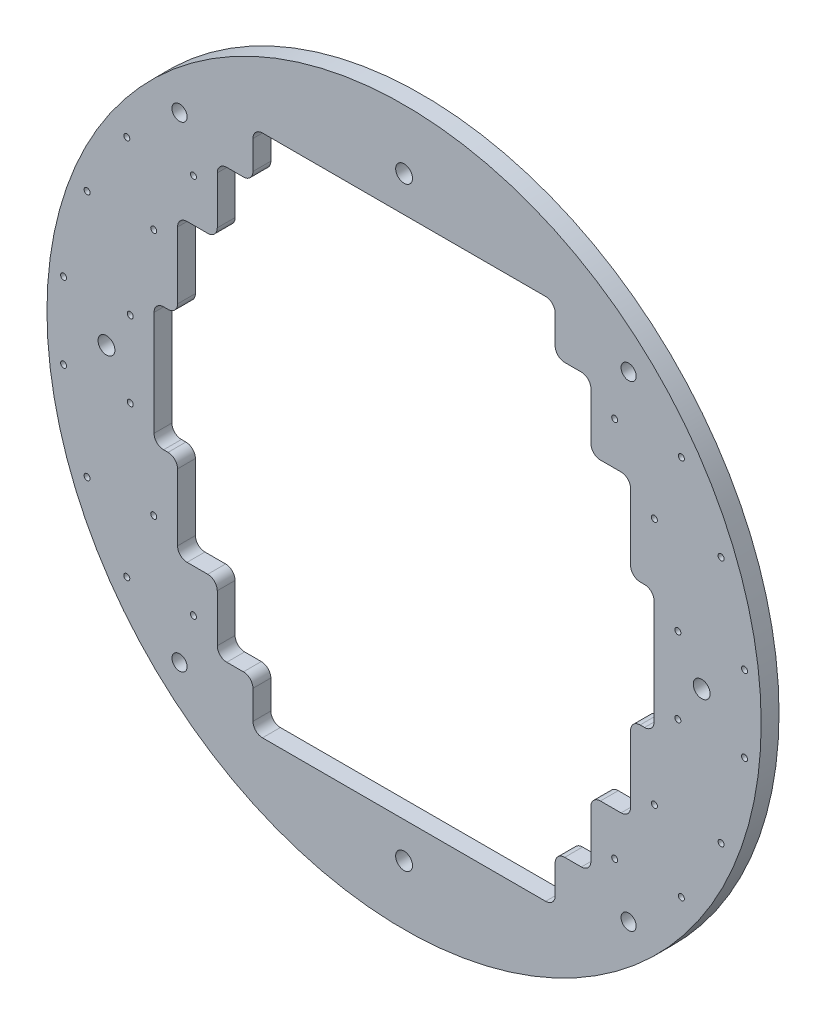
SolidWorks part; units mm, degrees
material "Delrin 2700 NC010, Low Viscosity Acetal Copolymer (SS)"
ref_plane "Front Plane" through (0, 0, 0) normal (0, 0, 1) x (1, 0, 0)
ref_plane "Top Plane" through (0, 0, 0) normal (0, 1, 0) x (1, 0, 0)
ref_plane "Right Plane" through (0, 0, 0) normal (1, 0, 0) x (0, 0, -1)
sketch "Sketch1" plane through (0, 0, 0) normal (0, 0, 1) x (1, 0, 0)
  circle A0 centre (0, 0) radius 95.25
  dimension "D1" = 190.5
extrude "Boss-Extrude1" add sketch "Sketch1" along normal blind 4.7625
hole_wizard "M2x0.4 Tapped Hole1" positions "Sketch3" profile "Sketch2" tap size "M2x0.4" standard "ANSI Metric"
sketch "Sketch3" plane through (0, 0, 4.7625) normal (0, 0, 1) x (1, 0, 0)
  line L0 (-84.5483, 33.02) -> (-66.7683, 33.02) construction
  line L1 (0, 0) -> (-124.3525, 0) construction
  line L2 (-73.9581, 50.8) -> (-56.1781, 50.8) construction
  line L3 (-90.8124, 10.16) -> (-73.0324, 10.16) construction
  line L5 (-73.9581, -50.8) -> (-56.1781, -50.8) construction
  line L6 (-84.5483, -33.02) -> (-66.7683, -33.02) construction
  line L7 (-90.8124, -10.16) -> (-73.0324, -10.16) construction
  line L8 (0, 0) -> (0, 116.1082) construction
  line L10 (73.9581, -50.8) -> (56.1781, -50.8) construction
  line L11 (84.5483, -33.02) -> (66.7683, -33.02) construction
  line L12 (90.8124, -10.16) -> (73.0324, -10.16) construction
  line L13 (90.8124, 10.16) -> (73.0324, 10.16) construction
  line L14 (84.5483, 33.02) -> (66.7683, 33.02) construction
  line L15 (73.9581, 50.8) -> (56.1781, 50.8) construction
  circle A0 centre (0, 0) radius 82.55 construction
  point P0 (-84.5483, 33.02)
  point P2 (-66.7683, 33.02)
  point P19 (-75.6583, 33.02)
  point P25 (-73.9581, 50.8)
  point P27 (-56.1781, 50.8)
  point P34 (-65.0681, 50.8)
  point P35 (-90.8124, 10.16)
  point P37 (-73.0324, 10.16)
  point P44 (-81.9224, 10.16)
  point P45 (-56.1781, -50.8)
  point P46 (-73.9581, -50.8)
  point P48 (-66.7683, -33.02)
  point P49 (-84.5483, -33.02)
  point P51 (-73.0324, -10.16)
  point P52 (-90.8124, -10.16)
  point P60 (56.1781, -50.8)
  point P61 (73.9581, -50.8)
  point P64 (66.7683, -33.02)
  point P65 (84.5483, -33.02)
  point P68 (90.8124, -10.16)
  point P70 (73.0324, -10.16)
  point P71 (90.8124, 10.16)
  point P73 (73.0324, 10.16)
  point P74 (84.5483, 33.02)
  point P76 (66.7683, 33.02)
  point P77 (56.1781, 50.8)
  point P78 (73.9581, 50.8)
  dimension "D4" = 165.1
  dimension "D1" = 17.78
  dimension "D2" = 33.02
  dimension "D3" = 17.78
  dimension "D5" = 50.8
  dimension "D6" = 17.78
  dimension "D7" = 10.16
sketch "Sketch2" plane through (-84.5483, 33.02, 4.7625) normal (1, 0, 0) x (0, -1, 0)
  line L0 (0, 0) -> (0, 5.334)
  line L1 (0, 5.334) -> (0.8, 5.334)
  line L2 (0.8, 5.334) -> (0.8, 0)
  line L5 (0.8, 0) -> (0, 0)
  line L10 (0, 5.334) -> (-0.8, 5.334) construction
  line L11 (0, -6.35) -> (0, 107.95) construction
  dimension "Tap Drill Dia." = 1.6
  dimension "Tap Drill Depth" = 5.334
  dimension "Drill Angle" = 180
cosmetic thread "Hole Thread1" parameters "D1"=4.064, "D2"=2
cosmetic thread "Hole Thread2" parameters "D1"=4.064, "D2"=2
cosmetic thread "Hole Thread3" parameters "D1"=4.064, "D2"=2
cosmetic thread "Hole Thread4" parameters "D1"=4.064, "D2"=2
cosmetic thread "Hole Thread5" parameters "D1"=4.064, "D2"=2
cosmetic thread "Hole Thread6" parameters "D1"=4.064, "D2"=2
cosmetic thread "Hole Thread7" parameters "D1"=4.064, "D2"=2
cosmetic thread "Hole Thread8" parameters "D1"=4.064, "D2"=2
cosmetic thread "Hole Thread9" parameters "D1"=4.064, "D2"=2
cosmetic thread "Hole Thread10" parameters "D1"=4.064, "D2"=2
cosmetic thread "Hole Thread11" parameters "D1"=4.064, "D2"=2
cosmetic thread "Hole Thread12" parameters "D1"=4.064, "D2"=2
cosmetic thread "Hole Thread13" parameters "D1"=4.064, "D2"=2
cosmetic thread "Hole Thread14" parameters "D1"=4.064, "D2"=2
cosmetic thread "Hole Thread15" parameters "D1"=4.064, "D2"=2
cosmetic thread "Hole Thread16" parameters "D1"=4.064, "D2"=2
cosmetic thread "Hole Thread17" parameters "D1"=4.064, "D2"=2
cosmetic thread "Hole Thread18" parameters "D1"=4.064, "D2"=2
cosmetic thread "Hole Thread19" parameters "D1"=4.064, "D2"=2
cosmetic thread "Hole Thread20" parameters "D1"=4.064, "D2"=2
cosmetic thread "Hole Thread21" parameters "D1"=4.064, "D2"=2
cosmetic thread "Hole Thread22" parameters "D1"=4.064, "D2"=2
cosmetic thread "Hole Thread23" parameters "D1"=4.064, "D2"=2
cosmetic thread "Hole Thread24" parameters "D1"=4.064, "D2"=2
hole_wizard "#12-24 Tapped Hole1" positions "Sketch7" profile "Sketch6" tap size "#12-24" standard "ANSI Inch"
sketch "Sketch7" plane through (0, 0, 4.7625) normal (0, 0, 1) x (1, 0, 0)
  circle A0 centre (0, 0) radius 79.375 construction
  point P0 (-79.375, 0)
  point P2 (0, 79.375)
  point P14 (79.375, 0)
  point P16 (0, -79.375)
  dimension "D1" = 158.75
sketch "Sketch6" plane through (-79.375, 0, 4.7625) normal (1, 0, 0) x (0, -1, 0)
  line L0 (0, 0) -> (0, 14.224)
  line L1 (0, 14.224) -> (2.2479, 14.224)
  line L2 (2.2479, 14.224) -> (2.2479, 0)
  line L5 (2.2479, 0) -> (0, 0)
  line L10 (0, 14.224) -> (-2.2479, 14.224) construction
  line L11 (0, -6.35) -> (0, 107.95) construction
  dimension "Tap Drill Dia." = 4.4958
  dimension "Tap Drill Depth" = 14.224
  dimension "Drill Angle" = 180
cosmetic thread "Hole Thread31" parameters "D1"=4.7625, "D2"=5.4864
cosmetic thread "Hole Thread32" parameters "D1"=4.7625, "D2"=5.4864
cosmetic thread "Hole Thread33" parameters "D1"=4.7625, "D2"=5.4864
cosmetic thread "Hole Thread34" parameters "D1"=4.7625, "D2"=5.4864
sketch "Sketch8" plane through (0, 0, 4.7625) normal (0, 0, 1) x (1, 0, 0)
  line L0 (-25.4, 50.8) -> (25.4, 50.8) construction
  line L1 (-25.4, 55.88) -> (25.4, 55.88)
  line L2 (-25.4, 45.72) -> (25.4, 45.72)
  line L3 (-38.1, 33.02) -> (38.1, 33.02) construction
  line L4 (-38.1, 38.1) -> (38.1, 38.1)
  line L5 (-38.1, 27.94) -> (38.1, 27.94)
  line L6 (-66.675, 16.51) -> (66.675, 16.51) construction
  line L7 (-66.675, 21.59) -> (66.675, 21.59)
  line L8 (-66.675, 11.43) -> (66.675, 11.43)
  line L9 (-73.9581, 50.8) -> (0, 50.8) construction
  line L10 (-84.5483, 33.02) -> (-38.1, 33.02) construction
  line L11 (-73.8324, 10.16) -> (73.0324, 10.16) construction
  line L12 (0, 0) -> (128.0225, 0) construction
  line L13 (-25.4, -50.8) -> (25.4, -50.8) construction
  line L14 (-25.4, -55.88) -> (25.4, -55.88)
  line L15 (-25.4, -45.72) -> (25.4, -45.72)
  line L16 (-38.1, -33.02) -> (38.1, -33.02) construction
  line L17 (-38.1, -38.1) -> (38.1, -38.1)
  line L18 (-38.1, -27.94) -> (38.1, -27.94)
  line L19 (-66.675, -3.81) -> (66.675, -3.81) construction
  line L20 (-66.675, -8.89) -> (66.675, -8.89)
  line L21 (-66.675, 1.27) -> (66.675, 1.27)
  line L22 (-73.8324, -10.16) -> (72.2324, -10.16) construction
  arc A0 (-25.4, 55.88) -> (-25.4, 45.72) centre (-25.4, 50.8) ccw
  arc A1 (25.4, 45.72) -> (25.4, 55.88) centre (25.4, 50.8) ccw
  arc A2 (-38.1, 38.1) -> (-38.1, 27.94) centre (-38.1, 33.02) ccw
  arc A3 (38.1, 27.94) -> (38.1, 38.1) centre (38.1, 33.02) ccw
  arc A4 (-66.675, 21.59) -> (-66.675, 11.43) centre (-66.675, 16.51) ccw
  arc A5 (66.675, 11.43) -> (66.675, 21.59) centre (66.675, 16.51) ccw
  circle A6 centre (-73.0324, 10.16) radius 0.8 construction
  circle A7 centre (-73.0324, -10.16) radius 0.8 construction
  circle A8 centre (73.0324, -10.16) radius 0.8 construction
  arc A9 (-25.4, -55.88) -> (-25.4, -45.72) centre (-25.4, -50.8) cw
  arc A10 (25.4, -45.72) -> (25.4, -55.88) centre (25.4, -50.8) cw
  arc A11 (-38.1, -38.1) -> (-38.1, -27.94) centre (-38.1, -33.02) cw
  arc A12 (38.1, -27.94) -> (38.1, -38.1) centre (38.1, -33.02) cw
  arc A13 (-66.675, -8.89) -> (-66.675, 1.27) centre (-66.675, -3.81) cw
  arc A14 (66.675, 1.27) -> (66.675, -8.89) centre (66.675, -3.81) cw
  point P2 (0, 50.8)
  point P8 (0, 33.02)
  point P15 (0, 16.51)
  point P35 (0, -50.8)
  point P42 (0, -33.02)
  point P49 (0, -3.81)
  dimension "D2" = 10.16
  dimension "D7" = 6.35
  dimension "D1" = 10.16
  dimension "D3" = 10.16
  dimension "D4" = 76.2
  dimension "D5" = 50.8
  dimension "D6" = 133.35
  dimension "D8" = 133.35
  dimension "D9" = 6.35
  dimension "D10" = 10.16
extrude "Cut-Extrude1" [suppressed] cut sketch "Sketch8" against normal through all
hole_wizard "#10-32 Tapped Hole1" positions "Sketch10" profile "Sketch9" tap size "#10-32" standard "ANSI Inch"
sketch "Sketch10" plane through (0, 0, 4.7625) normal (0, 0, 1) x (1, 0, 0)
  line L0 (-59.8919, 63.5) -> (59.8919, 63.5) construction
  point P0 (-59.8919, 63.5)
  point P2 (59.8919, 63.5)
  point P9 (0, 63.5)
  dimension "D1" = 63.5
  dimension "D2" = 119.7837
sketch "Sketch9" plane through (-59.8919, 63.5, 4.7625) normal (1, 0, 0) x (0, -1, 0)
  line L0 (0, 0) -> (0, 11.938)
  line L1 (0, 11.938) -> (2.0193, 11.938)
  line L2 (2.0193, 11.938) -> (2.0193, 0)
  line L5 (2.0193, 0) -> (0, 0)
  line L10 (0, 11.938) -> (-2.0193, 11.938) construction
  line L11 (0, -6.35) -> (0, 107.95) construction
  dimension "Tap Drill Dia." = 4.0386
  dimension "Tap Drill Depth" = 11.938
  dimension "Drill Angle" = 180
cosmetic thread "Hole Thread35" parameters "D1"=4.7625, "D2"=4.826
cosmetic thread "Hole Thread36" parameters "D1"=4.7625, "D2"=4.826
mirror "Mirror1" about plane through (0, 0, 0) normal (0, 1, 0) of "#10-32 Tapped Hole1"
sketch "Sketch11" plane through (0, 0, 4.7625) normal (0, 0, 1) x (1, 0, 0)
  line L1 (49.8281, -57.15) -> (-49.8281, -57.15)
  line L2 (49.8281, -57.15) -> (49.8281, 57.15)
  line L3 (49.8281, 57.15) -> (-49.8281, 57.15)
  line L4 (-49.8281, -57.15) -> (-49.8281, 57.15)
  line L5 (49.8281, -57.15) -> (-49.8281, 57.15) construction
  line L6 (49.8281, 57.15) -> (-49.8281, -57.15) construction
  line L7 (60.4183, -39.37) -> (-60.4183, -39.37)
  line L8 (60.4183, -39.37) -> (60.4183, 39.37)
  line L9 (60.4183, 39.37) -> (-60.4183, 39.37)
  line L10 (-60.4183, -39.37) -> (-60.4183, 39.37)
  line L11 (60.4183, -39.37) -> (-60.4183, 39.37) construction
  line L12 (60.4183, 39.37) -> (-60.4183, -39.37) construction
  line L13 (66.6824, -16.51) -> (-66.6824, -16.51)
  line L14 (66.6824, -16.51) -> (66.6824, 16.51)
  line L15 (66.6824, 16.51) -> (-66.6824, 16.51)
  line L16 (-66.6824, -16.51) -> (-66.6824, 16.51)
  line L17 (66.6824, -16.51) -> (-66.6824, 16.51) construction
  line L18 (66.6824, 16.51) -> (-66.6824, -16.51) construction
  circle A0 centre (-73.0324, 10.16) radius 0.8 construction
  circle A1 centre (-56.1781, 50.8) radius 0.8 construction
  circle A2 centre (-66.7683, 33.02) radius 0.8 construction
  point P0 (0, 0)
  point P6 (0, 0)
  point P15 (0, 0)
  dimension "D3" = 6.35
  dimension "D2" = 6.35
  dimension "D5" = 6.35
  dimension "D1" = 6.35
  dimension "D4" = 6.35
  dimension "D6" = 6.35
extrude "Cut-Extrude2" cut sketch "Sketch11" against normal through all contours L9 L2 L3 L4 | L15 L2 L9 L4 | L15 L4 L9 L10 | L15 L8 L9 L2 | L8 L15 L2 L13 | L14 L15 L8 L13 | L2 L15 L4 L13 | L4 L15 L10 L13 | L16 L13 L10 L15 | L4 L13 L10 L7 | L2 L13 L4 L7 | L8 L13 L2 L7 | L2 L7 L4 L1
sketch "Sketch12" plane through (0, 0, 4.7625) normal (0, 0, 1) x (1, 0, 0)
  line L0 (-49.8281, 39.37) -> (-49.8281, 57.15) construction
  line L1 (40.3031, -69.85) -> (-40.3031, -69.85)
  line L2 (40.3031, -69.85) -> (40.3031, 69.85)
  line L3 (40.3031, 69.85) -> (-40.3031, 69.85)
  line L4 (-40.3031, -69.85) -> (-40.3031, 69.85)
  line L5 (40.3031, -69.85) -> (-40.3031, 69.85) construction
  line L6 (40.3031, 69.85) -> (-40.3031, -69.85) construction
  circle A0 centre (0, 79.375) radius 2.2479 construction
  point P0 (0, 0)
  dimension "D1" = 9.525
  dimension "D2" = 9.525
extrude "Cut-Extrude3" cut sketch "Sketch12" against normal through all
fillet "Fillet1" radius 2.54 28 edges at (-66.6824, 16.51, 2.3813) (-66.6824, -16.51, 2.3813) (-60.4183, -16.51, 2.3813) (-60.4183, -39.37, 2.3813) (-49.8281, -39.37, 2.3813) (-49.8281, -57.15, 2.3813) (-40.3031, -57.15, 2.3813) (-40.3031, -69.85, 2.3813) (40.3031, -69.85, 2.3813) (40.3031, -57.15, 2.3813) (49.8281, -57.15, 2.3813) (49.8281, -39.37, 2.3813) (60.4183, -39.37, 2.3813) (60.4183, -16.51, 2.3813) (66.6824, -16.51, 2.3813) (66.6824, 16.51, 2.3813) (60.4183, 16.51, 2.3813) (60.4183, 39.37, 2.3813) (49.8281, 39.37, 2.3813) (49.8281, 57.15, 2.3813) (40.3031, 57.15, 2.3813) (40.3031, 69.85, 2.3813) (-40.3031, 69.85, 2.3813) (-49.8281, 57.15, 2.3813) (-60.4183, 39.37, 2.3813) (-40.3031, 57.15, 2.3813) (-49.8281, 39.37, 2.3813) (-60.4183, 16.51, 2.3813)
